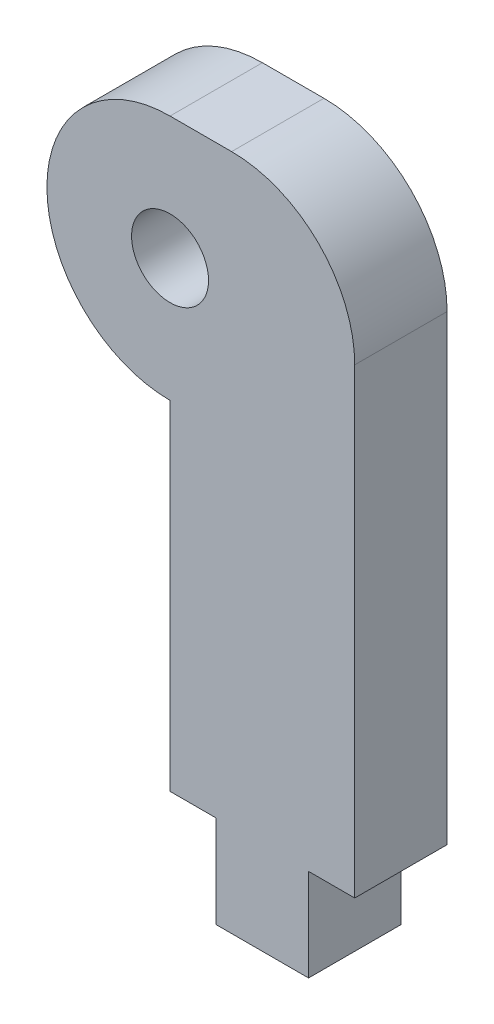
SolidWorks part; units mm, degrees
ref_plane "Front Plane" through (0, 0, 0) normal (0, 0, 1) x (1, 0, 0)
ref_plane "Top Plane" through (0, 0, 0) normal (0, 1, 0) x (1, 0, 0)
ref_plane "Right Plane" through (0, 0, 0) normal (1, 0, 0) x (0, 0, -1)
sketch "Sketch2" plane through (0, 0, 0) normal (0, 0, 1) x (1, 0, 0)
  line L0 (0, 38.3401) -> (0, -59.8736) construction
  line L1 (6, 4) -> (6, -15)
  line L2 (6, -15) -> (4.5, -15)
  line L3 (4.5, -15) -> (4.5, -18)
  line L4 (4.5, -18) -> (1.5, -18)
  line L5 (1.5, -18) -> (1.5, -15)
  line L6 (1.5, -15) -> (0, -15)
  line L7 (0, -15) -> (0, -4)
  line L8 (0, 4) -> (6, 4)
  line L10 (6, 38.3401) -> (6, -59.8736) construction
  arc A0 (0, 4) -> (0, -4) centre (0, 0) ccw
  circle A1 centre (0, 0) radius 1.25
  dimension "D2" = 2.5
  dimension "D3" = 8
  dimension "D4" = 0
  dimension "D5" = 19
  dimension "D6" = 3
  dimension "D7" = 1.5
  dimension "D8" = 3
  dimension "D1" = 6
extrude "Boss-Extrude1" add sketch "Sketch2" along normal blind 3
fillet "Fillet1" radius 4 1 edges at (6, 4, 1.5)
